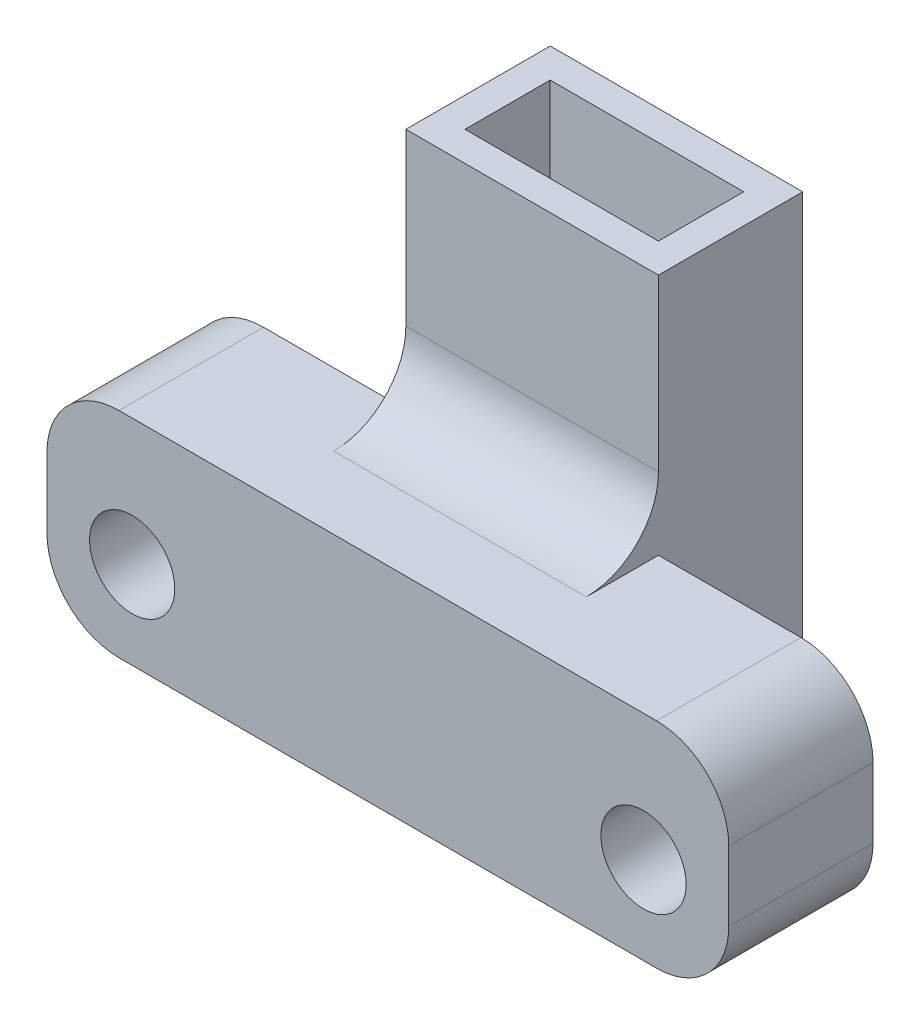
SolidWorks part; units mm, degrees
ref_plane "Front Plane" through (0, 0, 0) normal (0, 0, 1) x (1, 0, 0)
ref_plane "Top Plane" through (0, 0, 0) normal (0, 1, 0) x (1, 0, 0)
ref_plane "Right Plane" through (0, 0, 0) normal (1, 0, 0) x (0, 0, -1)
sketch "Sketch1" plane through (0, 0, 0) normal (0, 1, 0) x (1, 0, 0)
  line L1 (-4.445, -2.54) -> (4.445, -2.54)
  line L2 (-4.445, -2.54) -> (-4.445, 2.54)
  line L3 (-4.445, 2.54) -> (4.445, 2.54)
  line L4 (4.445, -2.54) -> (4.445, 2.54)
  line L5 (-4.445, -2.54) -> (4.445, 2.54) construction
  line L6 (-4.445, 2.54) -> (4.445, -2.54) construction
  point P0 (0, 0)
  dimension "D1" = 5.08
  dimension "D2" = 8.89
extrude "Boss-Extrude1" add sketch "Sketch1" along normal blind 16.08
sketch "Sketch2" plane through (0, 0, 2.54) normal (0, 0, 1) x (1, 0, 0)
  line L1 (-12, 7.5405) -> (12, 7.5405)
  line L2 (-12, 7.5405) -> (-12, 0)
  line L3 (-12, 0) -> (12, 0)
  line L4 (12, 7.5405) -> (12, 0)
  line L5 (-12, 7.5405) -> (12, 0) construction
  line L6 (-12, 0) -> (12, 7.5405) construction
  point P0 (0, 3.7703)
  dimension "D1" = 24
extrude "Boss-Extrude2" add sketch "Sketch2" along normal blind 5.08
sketch "Sketch3" plane through (0, 0, 7.62) normal (0, 0, 1) x (1, 0, 0)
  line L0 (-12, 0) -> (12, 0) construction
  line L1 (12, 7.5405) -> (-12, 7.5405) construction
  line L2 (0, 7.5405) -> (0, 0) construction
  circle A0 centre (-9, 3.0759) radius 1.5
  circle A1 centre (9, 3.0759) radius 1.5
  dimension "D1" = 3
  dimension "D2" = 18
  dimension "D3" = 3.0759
extrude "Cut-Extrude1" cut sketch "Sketch3" against normal through all
sketch "Sketch4" plane through (0, 16.08, 0) normal (0, 1, 0) x (1, 0, 0)
  line L1 (-3.405, -1.5) -> (3.405, -1.5)
  line L2 (-3.405, -1.5) -> (-3.405, 1.5)
  line L3 (-3.405, 1.5) -> (3.405, 1.5)
  line L4 (3.405, -1.5) -> (3.405, 1.5)
  line L5 (-3.405, -1.5) -> (3.405, 1.5) construction
  line L6 (-3.405, 1.5) -> (3.405, -1.5) construction
  line L7 (3.405, 1.5) -> (4.445, 1.5) construction
  line L8 (3.405, 1.5) -> (3.405, 2.54) construction
  line L9 (3.405, 2.54) -> (4.445, 2.54) construction
  line L10 (4.445, 1.5) -> (4.445, 2.54) construction
  point P0 (0, 0)
  dimension "D1" = 3
extrude "Cut-Extrude2" cut sketch "Sketch4" against normal through all contours L2 L3 L4 L1
fillet "Fillet1" radius 2.54 5 edges at (12, 0, 5.08) (-12, 0, 5.08) (0, 7.5405, 2.54) (12, 7.5405, 5.08) (-12, 7.5405, 5.08)
